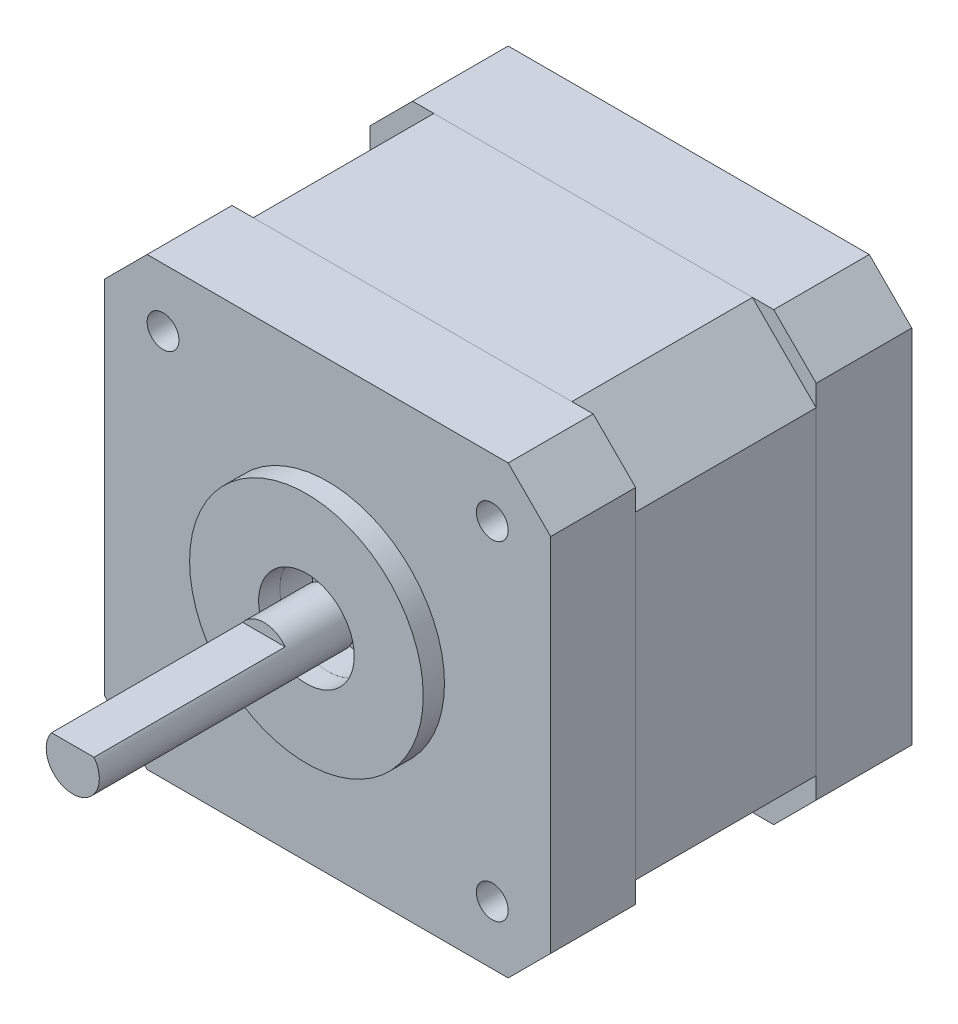
SolidWorks part; units mm, degrees
material "AISI 304"
ref_plane "前基準面" through (0, 0, 0) normal (0, 0, 1) x (1, 0, 0)
ref_plane "上基準面" through (0, 0, 0) normal (0, 1, 0) x (1, 0, 0)
ref_plane "右基準面" through (0, 0, 0) normal (1, 0, 0) x (0, 0, -1)
sketch "草圖1" plane through (0, 0, 0) normal (0, 0, 1) x (1, 0, 0)
  line L1 (-21, -21) -> (21, -21)
  line L2 (-21, -21) -> (-21, 21)
  line L3 (-21, 21) -> (21, 21)
  line L4 (21, -21) -> (21, 21)
  line L5 (-21, -21) -> (21, 21) construction
  line L6 (-21, 21) -> (21, -21) construction
  point P0 (0, 0)
  dimension "D1" = 42
  dimension "D2" = 42
extrude "填料-伸長1" add sketch "草圖1" along normal mid plane 17
chamfer "導角1" distance 6 angle 45 4 edges at (21, -21, 0) (-21, -21, 0) (-21, 21, 0) (21, 21, 0)
sketch "草圖15" plane through (0, 0, 8.5) normal (0, 0, 1) x (1, 0, 0)
  line L0 (15, 21) -> (-15, 21) construction
  line L1 (-21, -21) -> (21, -21)
  line L2 (-21, -21) -> (-21, 21)
  line L3 (-21, 21) -> (21, 21)
  line L4 (21, -21) -> (21, 21)
  line L5 (-21, -21) -> (21, 21) construction
  line L6 (-21, 21) -> (21, -21) construction
  line L7 (21, -15) -> (21, 15) construction
  point P0 (0, 0)
extrude "填料-伸長11" add sketch "草圖15" along normal blind 8 separate body
sketch "草圖16" plane through (0, 0, -8.5) normal (0, 0, -1) x (-1, 0, 0)
  line L1 (-21, -21) -> (21, -21)
  line L2 (-21, -21) -> (-21, 21)
  line L3 (-21, 21) -> (21, 21)
  line L4 (21, -21) -> (21, 21)
  line L5 (-21, -21) -> (21, 21) construction
  line L6 (-21, 21) -> (21, -21) construction
  line L8 (-15, 21) -> (15, 21) construction
  line L9 (21, 15) -> (21, -15) construction
  point P0 (0, 0)
extrude "填料-伸長12" add sketch "草圖16" along normal blind 9 separate body
chamfer "導角2" distance 4 angle 45 4 edges at (-21, -21, 12.5) (21, -21, 12.5) (21, 21, 12.5) (-21, 21, 12.5)
chamfer "導角3" distance 4 angle 45 4 edges at (-21, -21, -13) (21, -21, -13) (-21, 21, -13) (21, 21, -13)
sketch "草圖2" plane through (0, 0, 16.5) normal (0, 0, 1) x (1, 0, 0)
  circle A0 centre (0, 0) radius 11
  dimension "D1" = 22
extrude "填料-伸長2" add sketch "草圖2" along normal blind 2
sketch "草圖3" plane through (0, 0, 18.5) normal (0, 0, 1) x (1, 0, 0)
  circle A0 centre (0, 0) radius 4.5
  dimension "D1" = 9
extrude "除料-伸長1" cut sketch "草圖3" along direction (0, 0, -1) on the side against the normal blind 5
sketch "草圖6" plane through (0, 0, 16.5) normal (0, 0, 1) x (1, 0, 0)
  circle A0 centre (0, 0) radius 2.5
  dimension "D1" = 5
extrude "填料-伸長9" add sketch "草圖6" along direction (0, 0, 1) on the side of the normal offset from surface (24 mm away) 22 separate body
sketch "草圖8" plane through (0, 0, 16.5) normal (0, 0, 1) x (1, 0, 0)
  line L0 (0, 0) -> (0, 15.5) construction
  line L1 (0, 15.5) -> (-15.5, 15.5) construction
  circle A0 centre (-15.5, 15.5) radius 1.5
  dimension "D3" = 3
  dimension "D1" = 15.5
  dimension "D2" = 15.5
extrude "除料-伸長3" cut sketch "草圖8" against normal blind 4.5
sketch "草圖11" plane through (0, 0, 40.5) normal (0, 0, 1) x (1, 0, 0)
  line L0 (-2, 1.5) -> (2, 1.5)
  circle A0 centre (0, 0) radius 2.5 construction
  arc A1 (2, 1.5) -> (-2, 1.5) centre (0, 0) ccw
  point P5 (0, 1.5)
  point P6 (0, 2.5)
  dimension "D1" = 1
extrude "除料-伸長4" cut sketch "草圖11" against normal blind 18
pattern_circular "環狀複製排列1" count 4 over 360 about axis through (0, 0, 0) along (0, 0, 1) of "除料-伸長3"
